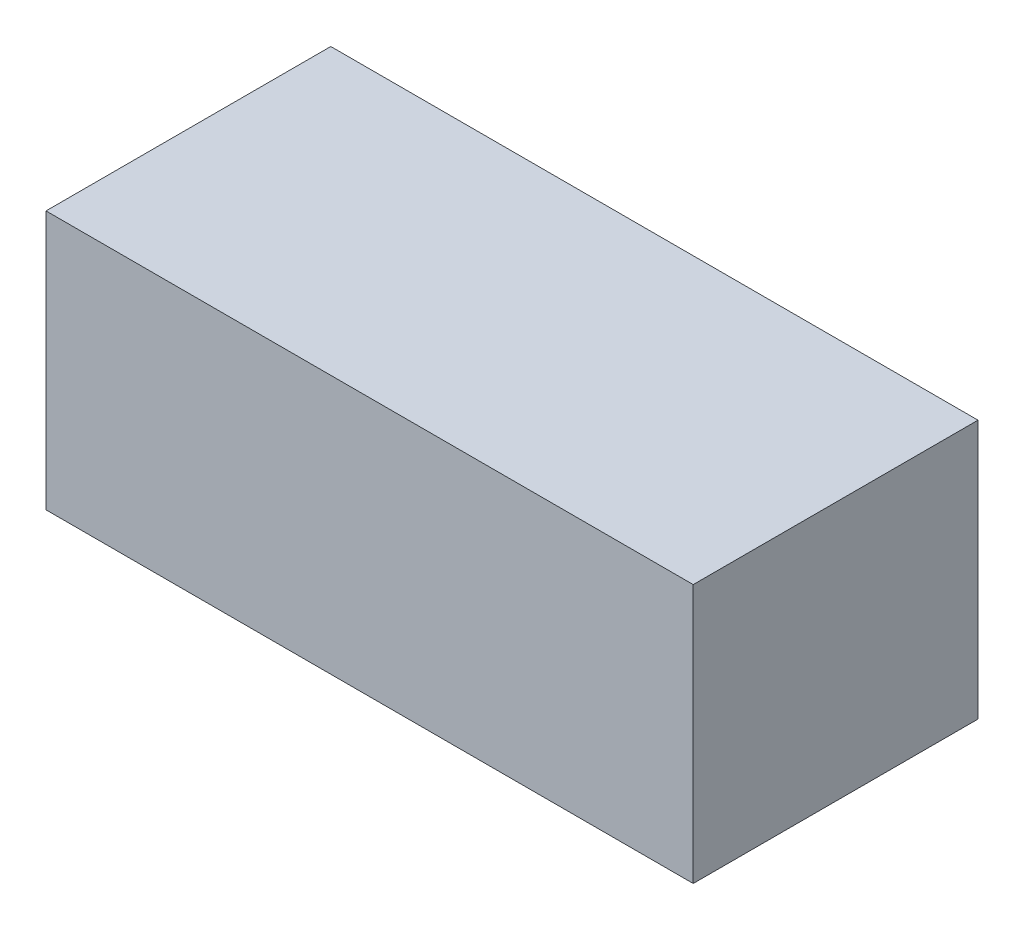
SolidWorks part; units mm, degrees
ref_plane "Front Plane" through (0, 0, 0) normal (0, 0, 1) x (1, 0, 0)
ref_plane "Top Plane" through (0, 0, 0) normal (0, 1, 0) x (1, 0, 0)
ref_plane "Right Plane" through (0, 0, 0) normal (1, 0, 0) x (0, 0, -1)
sketch "Sketch1" plane through (0, 0, 0) normal (0, 1, 0) x (1, 0, 0)
  line L1 (0, 0) -> (-500, 0)
  line L2 (0, 0) -> (0, 220)
  line L3 (0, 220) -> (-500, 220)
  line L4 (-500, 0) -> (-500, 220)
  dimension "D1" = 500
  dimension "D2" = 220
extrude "Extrude1" add sketch "Sketch1" along normal blind 200
